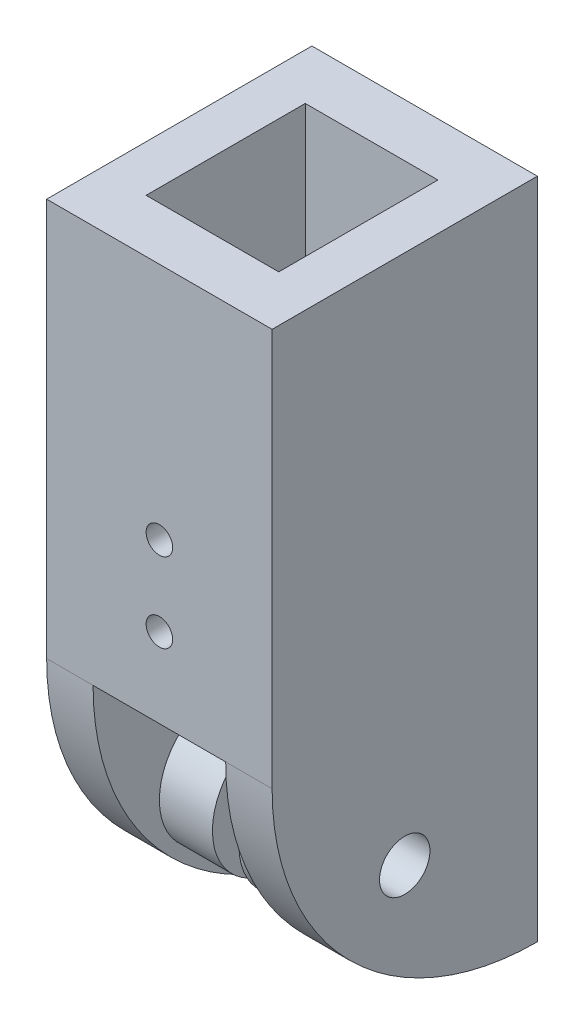
SolidWorks part; units mm, degrees
ref_plane "Front Plane" through (0, 0, 0) normal (0, 0, 1) x (1, 0, 0)
ref_plane "Top Plane" through (0, 0, 0) normal (0, 1, 0) x (1, 0, 0)
ref_plane "Right Plane" through (0, 0, 0) normal (1, 0, 0) x (0, 0, -1)
sketch "Sketch1" plane through (0, 0, 0) normal (0, 1, 0) x (1, 0, 0)
  line L1 (-4.5, -5) -> (4.5, -5)
  line L2 (-4.5, -5) -> (-4.5, 5)
  line L3 (-4.5, 5) -> (4.5, 5)
  line L4 (4.5, -5) -> (4.5, 5)
  line L5 (-4.5, -5) -> (4.5, 5) construction
  line L6 (-4.5, 5) -> (4.5, -5) construction
  line L7 (-2.5, -3) -> (2.5, -3)
  line L8 (-2.5, -3) -> (-2.5, 3)
  line L9 (-2.5, 3) -> (2.5, 3)
  line L10 (2.5, -3) -> (2.5, 3)
  line L11 (-2.5, -3) -> (2.5, 3) construction
  line L12 (-2.5, 3) -> (2.5, -3) construction
  point P0 (0, 0)
  point P6 (0, 0)
  dimension "D1" = 10
  dimension "D2" = 9
  dimension "D3" = 2
  dimension "D4" = 2
extrude "Boss-Extrude1" add sketch "Sketch1" along normal blind 15
sketch "Sketch2" plane through (4.5, 0, 0) normal (1, 0, 0) x (0, 0, -1)
  line L0 (5, 0) -> (5, -20)
  line L2 (-5, 0) -> (5, 0)
  arc A0 (-5, 0) -> (5, -10) centre (5, 0) ccw
  line M2 (-5, 0) -> (5, 0)
  dimension "D1" = 20
extrude "Boss-Extrude2" add sketch "Sketch2" against normal blind 2 contours A0 L0 M2
mirror "Mirror1" about plane through (0, 0, 0) normal (1, 0, 0) of "Boss-Extrude2"
sketch "Sketch3" plane through (4.5, 0, 0) normal (1, 0, 0) x (0, 0, -1)
  line L0 (4.95, 0) -> (-4.95, 0) construction
  line L1 (5, 15) -> (5, -10) construction
  circle A0 centre (0, -5) radius 0.95
  dimension "D1" = 1.9
  dimension "D2" = 5
  dimension "D3" = 5
extrude "Cut-Extrude2" cut sketch "Sketch3" against normal through all both and the other way through all
sketch "Sketch5" plane through (-2.5, 0, 0) normal (1, 0, 0) x (0, 0, -1)
  circle A0 centre (0, -5) radius 1.5
  circle A1 centre (0, -5) radius 0.95
  dimension "D1" = 3
  dimension "D2" = 1.9
extrude "Boss-Extrude3" add sketch "Sketch5" along normal up to surface (5 mm away) up to face at (2.5, -5, 0.95)
sketch "Sketch6" plane through (0, 0, 5) normal (0, 0, 1) x (1, 0, 0)
  line L0 (0, -5.5) -> (0, 5.5) construction
  line L1 (4.95, 0) -> (-4.95, 0) construction
  circle A0 centre (0, 3) radius 0.5
  circle A1 centre (0, 6) radius 0.5
  dimension "D1" = 1
  dimension "D2" = 1
  dimension "D3" = 3
  dimension "D4" = 3
extrude "Cut-Extrude3" cut sketch "Sketch6" against normal through all
sketch "Sketch7" plane through (0, 0, 5) normal (0, 0, 1) x (1, 0, 0)
  line L1 (-4.5, 15) -> (-4.25, 15)
  line L2 (-4.5, 15) -> (-4.5, -10.6833)
  line L3 (-4.5, -10.6833) -> (-4.25, -10.6833)
  line L4 (-4.25, 15) -> (-4.25, -10.6833)
  line L5 (4.5, 15) -> (4.25, 15)
  line L6 (4.5, 15) -> (4.5, -12.4068)
  line L7 (4.5, -12.4068) -> (4.25, -12.4068)
  line L8 (4.25, 15) -> (4.25, -12.4068)
  dimension "D1" = 0.25
  dimension "D2" = 0.25
extrude "Cut-Extrude4" cut sketch "Sketch7" against normal through all both and the other way through all
sketch "Sketch8" plane through (2.5, 0, 0) normal (-1, 0, 0) x (0, 0, 1)
  circle A0 centre (0, -5) radius 2.5
  circle A1 centre (0, -5) radius 1.5
  dimension "D1" = 5
extrude "Boss-Extrude4" add sketch "Sketch8" along normal blind 2
mirror "Mirror2" about plane through (0, 0, 0) normal (1, 0, 0) of "Boss-Extrude4"
